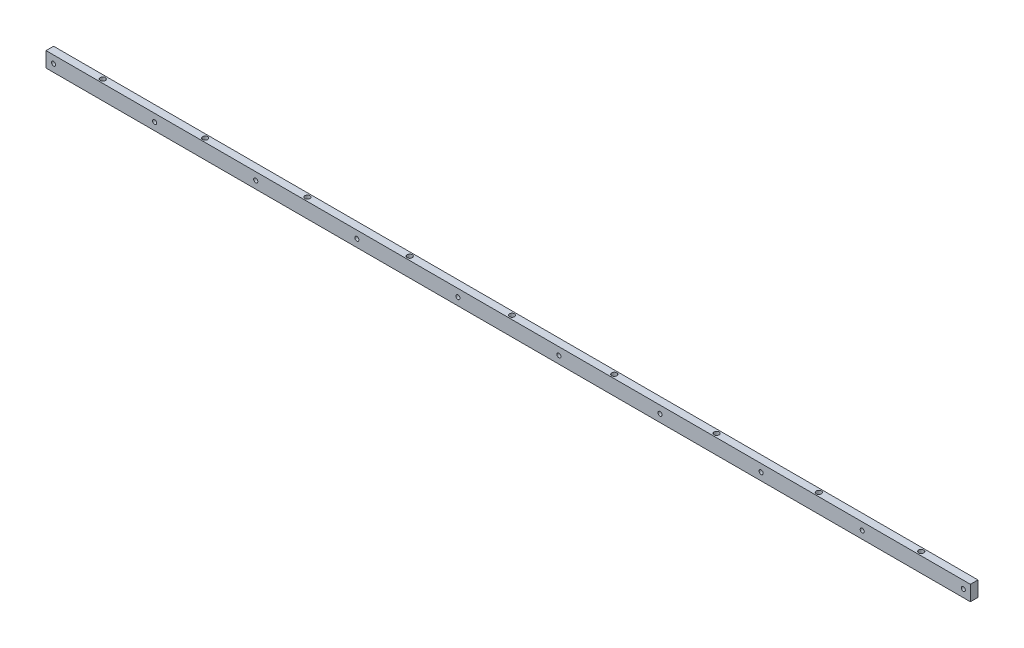
SolidWorks part; units mm, degrees
material "1060 Alloy"
ref_plane "Front Plane" through (0, 0, 0) normal (0, 0, 1) x (1, 0, 0)
ref_plane "Top Plane" through (0, 0, 0) normal (0, 1, 0) x (1, 0, 0)
ref_plane "Right Plane" through (0, 0, 0) normal (1, 0, 0) x (0, 0, -1)
sketch "Sketch1" plane through (0, 0, 0) normal (0, 0, 1) x (1, 0, 0)
  line L0 (0, 12.7) -> (1549.4, 12.7) construction
  line L1 (0, 0) -> (1549.4, 0)
  line L2 (0, 0) -> (0, 25.4)
  line L3 (0, 25.4) -> (1549.4, 25.4)
  line L4 (1549.4, 0) -> (1549.4, 25.4)
  circle A0 centre (12.7, 12.7) radius 3.429
  circle A1 centre (182.118, 12.7) radius 3.429
  circle A2 centre (351.536, 12.7) radius 3.429
  circle A3 centre (520.954, 12.7) radius 3.429
  circle A4 centre (690.372, 12.7) radius 3.429
  circle A5 centre (859.79, 12.7) radius 3.429
  circle A6 centre (1029.208, 12.7) radius 3.429
  circle A7 centre (1198.626, 12.7) radius 3.429
  circle A8 centre (1368.044, 12.7) radius 3.429
  circle A9 centre (1537.462, 12.7) radius 3.429
  dimension "D3" = 6.858
  dimension "D4" = 12.7
  dimension "D6" = 169.418
  dimension "D1" = 1549.4
  dimension "D2" = 25.4
  dimension "D5" = 10
extrude "Boss-Extrude1" add sketch "Sketch1" against normal blind 12.7
sketch "Sketch2" plane through (0, 25.4, 0) normal (0, 1, 0) x (1, 0, 0)
  line L0 (0, 6.35) -> (1549.4, 6.35) construction
  line L1 (0, 12.7) -> (0, 0) construction
  line L2 (1549.4, 12.7) -> (1549.4, 0) construction
  point P6 (88.9, 6.35)
  dimension "D1" = 88.9
hole_wizard "Hole1" positions "3DSketch1" profile "Sketch3" legacy end condition through all
sketch3d "3DSketch1"
  point P0 (88.9, 25.4, -6.35)
sketch "Sketch3" plane through (88.9, 25.4, -6.35) normal (1, 0, 0) x (0, 0, 1)
  line L0 (0, 0) -> (0, 25.4)
  line L1 (0, 25.4) -> (2.794, 25.4)
  line L2 (2.794, 25.4) -> (2.794, 10.922)
  line L3 (2.794, 10.922) -> (4.318, 10.922)
  line L4 (4.318, 10.922) -> (4.318, 0)
  line L5 (4.318, 0) -> (0, 0)
  line L6 (0, 110) -> (0, -10) construction
  dimension "Diameter" = 5.588
  dimension "Depth" = 25.4
  dimension "C-Bore Diameter" = 8.636
  dimension "C-Bore Depth" = 10.922
pattern_linear "LPattern1" count 9 spacing 171.45 along (1, 0, 0) of "Hole1"
sketch "Sketch4" plane through (0, 0, 0) normal (0, -1, 0) x (-1, 0, 0)
  line L0 (0, 6.35) -> (-1549.4, 6.35) construction
  line L1 (0, 12.7) -> (0, 0) construction
  line L2 (-1549.4, 12.7) -> (-1549.4, 0) construction
  point P6 (-88.9, 6.35)
  dimension "D1" = 88.9
hole_wizard "Hole2" positions "3DSketch2" profile "Sketch5" legacy end condition through all
sketch3d "3DSketch2"
  point P0 (88.9, 0, -6.35)
sketch "Sketch5" plane through (88.9, 0, -6.35) normal (1, 0, 0) x (0, 0, -1)
  line L0 (0, 0) -> (0, 25.4)
  line L1 (0, 25.4) -> (2.794, 25.4)
  line L2 (2.794, 25.4) -> (2.794, 9.906)
  line L3 (2.794, 9.906) -> (2.54, 9.906)
  line L4 (2.54, 9.906) -> (2.54, 0)
  line L5 (2.54, 0) -> (0, 0)
  line L6 (0, 110) -> (0, -10) construction
  dimension "Diameter" = 5.588
  dimension "Depth" = 25.4
  dimension "C-Bore Diameter" = 5.08
  dimension "C-Bore Depth" = 9.906
pattern_linear "LPattern2" count 9 spacing 171.45 along (1, 0, 0) of "Hole2"
